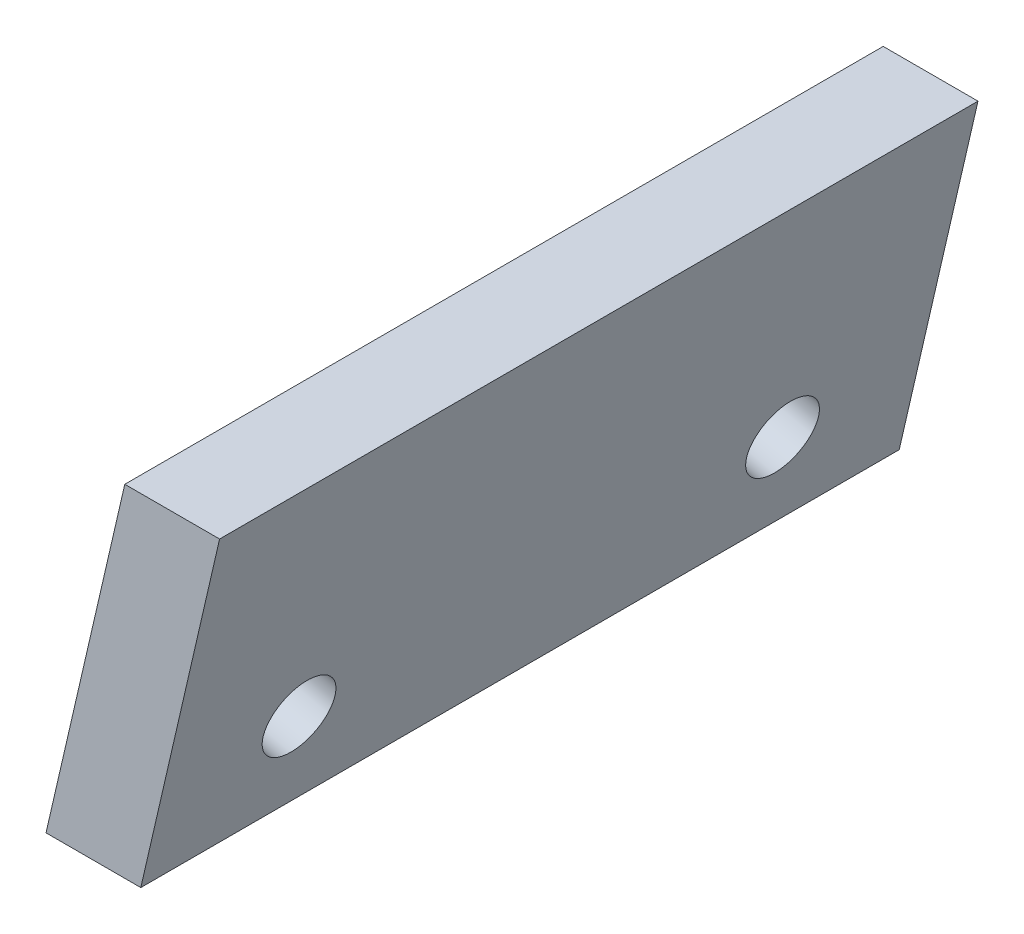
SolidWorks part; units mm, degrees
ref_plane "Front Plane" through (0, 0, 0) normal (0, 0, 1) x (1, 0, 0)
ref_plane "Top Plane" through (0, 0, 0) normal (0, 1, 0) x (1, 0, 0)
ref_plane "Right Plane" through (0, 0, 0) normal (1, 0, 0) x (0, 0, -1)
sketch "Sketch2" plane through (0, 0, 0) normal (0, 0, 1) x (1, 0, 0)
  line L0 (0, 0) -> (2.5, 0)
  line L1 (0, 0) -> (2.0778, 9)
  line L2 (2.5, 0) -> (4.5778, 9)
  line L3 (4.5778, 9) -> (2.0778, 9)
  line L4 (2.5, 0) -> (7.5011, 0) construction
  dimension "D1" = 9
  dimension "D2" = 2.5
  dimension "D3" = 77
extrude "Boss-Extrude2" add sketch "Sketch2" along normal blind 20
sketch "Sketch4" plane through (0, 0, 0) normal (-0.9744, 0.225, 0) x (0, 0, 1)
  line L0 (0, 9.2367) -> (0, 0) construction
  line L1 (20, 9.2367) -> (20, 0) construction
  line L2 (20, 0) -> (0, 0) construction
  circle A0 centre (3.625, 3) radius 0.95
  circle A1 centre (16.375, 3) radius 0.95
  dimension "D1" = 3.625
  dimension "D2" = 3.625
  dimension "D3" = 3
  dimension "D4" = 3
  dimension "D5" = 1.9
  dimension "D6" = 1.9
extrude "Cut-Extrude1" cut sketch "Sketch4" against normal through all
